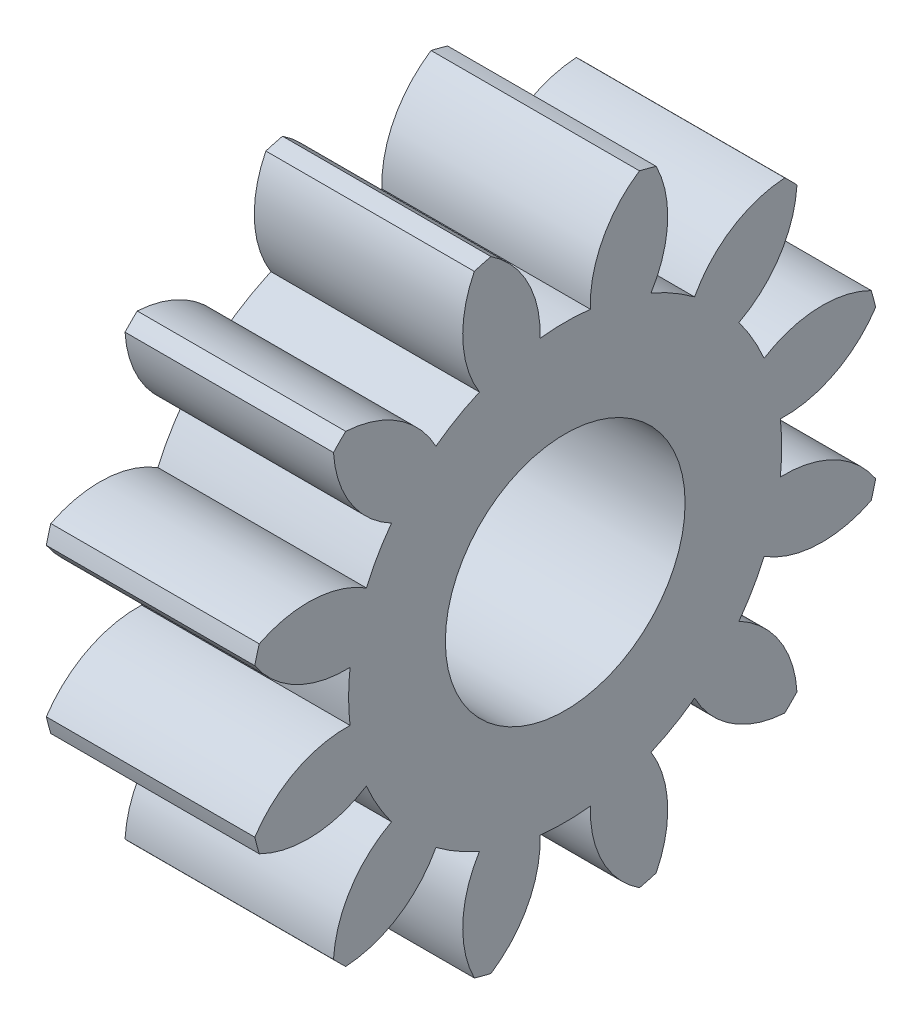
SolidWorks part; units mm, degrees
material "PLA personnalisé"
ref_plane "Plane1" through (0, 0, 0) normal (0, 0, 1) x (1, 0, 0)
ref_plane "Plane2" through (0, 0, 0) normal (0, 1, 0) x (1, 0, 0)
ref_plane "Plane3" through (0, 0, 0) normal (1, 0, 0) x (0, 0, -1)
other "Configuration Table"
sketch "HoldingSke" plane through (0, 0, 0) normal (0, 1, 0) x (1, 0, 0)
  line L0 (0, 0) -> (0.5589, -0.1188)
  line L1 (-15, 0) -> (100, 0) construction
  line L2 (0, 0) -> (-2.1039, 2.3779)
  line L3 (0, 0) -> (-11.863, 4.5341)
  line L4 (0, 0) -> (8.4473, 1.7955)
  line L5 (0, 0) -> (-14.9912, -5.5913)
  line L6 (0, 0) -> (-6.6317, -4.4744)
  line L7 (-2.1039, 2.3779) -> (1.3401, 18.0029)
  line L8 (-76.2, 54.61) -> (-74.8, 54.61)
  line L9 (-71.009, 38.7566) -> (-53.1078, 45.2721)
  line L10 (-76.2, 71.12) -> (104.1128, 71.12)
  line L11 (0, 0) -> (-8, 0)
  line L12 (-76.2, 101.6) -> (-76.147, 101.6)
  line L13 (24.9733, 27.94) -> (52.9518, 28.4284)
  line L14 (24.9733, 27.94) -> (24.9743, 27.94)
  line L15 (24.9733, 27.94) -> (100.4006, 29.5858)
  line L16 (-63.627, -1.75) -> (-12.827, -1.75)
  circle A0 centre (0, 0) radius 4.5
  circle A1 centre (0, 0) radius 8.3115
  circle A2 centre (0, 0) radius 37.5
  circle A3 centre (0, 0) radius 4.5
  dimension "MHD" = 16.623
  dimension "Hub_dia" = 75
  dimension "Bore" = 9
  dimension "MBD" = 9
  dimension "Num_teeth" = 12
  dimension "Pitch" = 0.5714
  dimension "Overall_len" = 16
  dimension "Show_teeth" = 12
  dimension "Thickness" = 8
  dimension "OAL" = 16.0001
  dimension "T_dim" = 1.4
  dimension "Ap" = 20
  dimension "H" = 19.05
  dimension "Pitch_radius" = 180.3128
  dimension "Width" = 8
  dimension "Backlash" = 0.053
  dimension "Addendum_fac" = 1
  dimension "Dedendum_fac" = 1.25
  dimension "Clearance_fac" = 0.25
  dimension "Dedendum_add" = 0.001
  dimension "Module" = 1.75
sketch "BasProSke" plane through (0, 0, 0) normal (0, 1, 0) x (1, 0, 0)
  line L0 (-10, 0) -> (60, 0) construction
  line L1 (0, 0) -> (0, 12.25)
  line L2 (0, 0) -> (8, 0)
  line L3 (8, 0) -> (8, 12.25)
  line L4 (8, 12.25) -> (0, 12.25)
  dimension "Thickness" = 8
  dimension "Diameter" = 24.5
revolve "Base-Revolve" add sketch "BasProSke" angle 360 about L0
sketch "TooCutSke" plane through (0, 0, 0) normal (1, 0, 0) x (0, 0, -1)
  line L1 (0, 0) -> (0, 107) construction
  line L2 (0, 0) -> (-1.4632, 10.3976) construction
  line L3 (0, 0) -> (-5.3948, 20.1337) construction
  line L4 (-1.4632, 10.3976) -> (-2.6974, 10.0668) construction
  arc A0 (0.9651, 8.2553) -> (-0.9651, 8.2553) centre (0, 0) ccw
  arc A1 (2.8783, 11.9332) -> (-2.8783, 11.9332) centre (0, 0) ccw
  circle A2 centre (0, 0) radius 10.5 construction
  circle A3 centre (0, 0) radius 9.8668 construction
  arc A4 (-0.9651, 8.2553) -> (-2.8783, 11.9332) centre (-5.1623, 8.4085) ccw
  arc A5 (2.8783, 11.9332) -> (0.9651, 8.2553) centre (5.1623, 8.4085) ccw
  dimension "Root_dia" = 16.623
  dimension "Overcut_dia" = 24.5508
  dimension "Pitch_dia" = 21
  dimension "Base_dia" = 19.7335
  dimension "Flank_rad" = 4.2
  dimension "Half_ang" = 15
  dimension "Half_CT" = 1.2778
extrude "ToothCut" cut sketch "TooCutSke" along normal through all
fillet "Breaks" [suppressed] radius 0.035
fillet "RootFillets" [suppressed] radius 0.4385
pattern_circular "TeethCuts" count 12 every 30 about axis through (-10, 0, 0) along (1, 0, 0) of "ToothCut", "RootFillets", "Breaks"
sketch "HubNeaOneSke" plane through (0, 0, 0) normal (-1, 0, 0) x (0, 0, 1)
  circle A0 centre (0, 0) radius 8.3115
  dimension "Diameter" = 16.623
extrude "HubNearOne" add sketch "HubNeaOneSke" along normal blind 8.0001
sketch "HubNeaBotSke" plane through (0, 0, 0) normal (-1, 0, 0) x (0, 0, 1)
  circle A0 centre (0, 0) radius 8.3115
  dimension "Diameter" = 16.623
extrude "HubNearBoth" [suppressed] add sketch "HubNeaBotSke" along normal blind 4
ref_plane "FarPln" through (8, 0, 0) normal (1, 0, 0) x (0, 0, -1)
sketch "HubFarSke" plane through (8, 0, 0) normal (1, 0, 0) x (0, 0, -1)
  circle A0 centre (0, 0) radius 8.3115
  dimension "Diameter" = 16.623
extrude "HubFar" [suppressed] add sketch "HubFarSke" along normal blind 4
sketch "BorSke" plane through (0, 0, 0) normal (1, 0, 0) x (0, 0, -1)
  circle A0 centre (0, 0) radius 4.5
  dimension "Diameter" = 9
extrude "Bore" cut sketch "BorSke" along normal mid plane 32.0001
sketch "KeySke" plane through (0, 0, 0) normal (1, 0, 0) x (0, 0, -1)
  line L0 (-1.5, 0) -> (-1.5, 5.9)
  line L1 (-1.5, 5.9) -> (1.5, 5.9)
  line L2 (1.5, 5.9) -> (1.5, 0)
  line L3 (0, 0) -> (0, 34) construction
  line L4 (-1.5, 0) -> (1.5, 0)
  dimension "Offset" = 5.9
  dimension "Width" = 3
extrude "Keyway" [suppressed] cut sketch "KeySke" along normal mid plane 32.0001
pattern_circular "Keyway2" [suppressed] count 2 every 90 about axis through (-10, 0, 0) along (1, 0, 0)
sketch "Esquisse1" plane through (-8.0001, 0, 0) normal (-1, 0, 0) x (0, 0, 1)
  circle A0 centre (0, 0) radius 8.3115
extrude "Enlèv. mat.-Extru.1" cut sketch "Esquisse1" against normal blind 8
sketch "Esquisse2" plane through (8, 0, 0) normal (1, 0, 0) x (0, 0, -1)
  circle A0 centre (0, 0) radius 4.275
  circle A1 centre (0, 0) radius 4.5
  dimension "D1" = 8.55
extrude "Boss.-Extru.1" add sketch "Esquisse2" against normal blind 8
sketch "Esquisse3" plane through (-0.0001, 0, 0) normal (-1, 0, 0) x (0, 0, 1)
  circle A0 centre (0, 0) radius 4.6
  dimension "D1" = 9.2
extrude "Enlèv. mat.-Extru.2" cut sketch "Esquisse3" against normal blind 10
equation "' \"Module@HoldingSke\" = 6.35"
equation "' \"Num_teeth@HoldingSke\" = 12"
equation "' \"Ap@HoldingSke\" =  20"
equation "' \"Ap@HoldingSke\" = 20"
equation "' \"Width@HoldingSke\" = 0.5 * 25.4"
equation "' \"Hub_dia@HoldingSke\"= 1 * 25.4"
equation "' \"Hub_dia@HoldingSke\" = 1 * 25.4"
equation "' \"Overall_len@HoldingSke\" = 1.0 * 25.4"
equation "' \"Bore@HoldingSke\" = 0.75 * 25.4"
equation "' \"T_dim@HoldingSke\" = 0.1 * 25.4"
equation "' \"Width@KeySke\" = 0.25 * 25.4"
equation "' \"Show_teeth@HoldingSke\" = 13"
equation "' \"Backlash@HoldingSke\" = 0.009 * 25.4"
equation "' \"Addendum_fac@HoldingSke\" = 1.0"
equation "' \"Dedendum_fac@HoldingSke\" = 1.25"
equation "' \"Dedendum_add@HoldingSke\" = 0.00005 * 25.4"
equation "' \"Clearance_fac@HoldingSke\" = 0.25"
equation "\"Pitch@HoldingSke\" = 1 / \"Module@HoldingSke\""
equation "\"Overcut_dia@TooCutSke\" = (\"Num_teeth@HoldingSke\" + 2 * \"Addendum_fac@HoldingSke\") / \"Pitch@HoldingSke\" + 0.002 * 25.4"
equation "\"Pitch_dia@TooCutSke\" = \"Num_teeth@HoldingSke\" / \"Pitch@HoldingSke\""
equation "\"Base_dia@TooCutSke\" = \"Num_teeth@HoldingSke\" / \"Pitch@HoldingSke\" * cos((\"Ap@HoldingSke\"  * 3.14159265 / 180))"
equation "\"Root_dia@TooCutSke\" = (\"Num_teeth@HoldingSke\" + 2) / \"Pitch@HoldingSke\" - 2 * (\"Addendum_fac@HoldingSke\" + \"Dedendum_fac@HoldingSke\") / \"Pitch@HoldingSke\" - \"Dedendum_add@HoldingSke\" * 2"
equation "\"Half_ang@TooCutSke\" = 180 / \"Num_teeth@HoldingSke\""
equation "\"Half_CT@TooCutSke\" = \"Num_teeth@HoldingSke\" / \"Pitch@HoldingSke\" * sin((3.14159265 / 2 / \"Num_teeth@HoldingSke\")) / 2 - 7 * \"Backlash@HoldingSke\" / 4"
equation "\"Flank_rad@TooCutSke\" = \"Num_teeth@HoldingSke\" / \"Pitch@HoldingSke\" / 5"
equation "\"Radius@RootFillets\" = \"Clearance_fac@HoldingSke\" / \"Pitch@HoldingSke\" + \"Dedendum_add@HoldingSke\""
equation "\"Break_rad@Breaks\" = 0.02 / \"Pitch@HoldingSke\""
equation "\"Thickness@HoldingSke\" = \"Width@HoldingSke\""
equation "\"OAL@HoldingSke\" = \"Thickness@HoldingSke\""
equation "\"MHD@HoldingSke\" = (\"Num_teeth@HoldingSke\" + 2) / \"Pitch@HoldingSke\" - 2 * (\"Addendum_fac@HoldingSke\" + \"Dedendum_fac@HoldingSke\")  / \"Pitch@HoldingSke\" - \"Dedendum_add@HoldingSke\" * 2"
equation "\"MBD@HoldingSke\" = (\"Num_teeth@HoldingSke\" + 2) / \"Pitch@HoldingSke\" - 2 * (\"Addendum_fac@HoldingSke\" + \"Dedendum_fac@HoldingSke\")  / \"Pitch@HoldingSke\" - \"Dedendum_add@HoldingSke\" * 2 - 0.002 * 25.4"
equation "\"MHD@HoldingSke\" = ((sgn( \"MHD@HoldingSke\" - \"Hub_dia@HoldingSke\" )-1)*( \"MHD@HoldingSke\" - \"Hub_dia@HoldingSke\" ))/-2+ \"Hub_dia@HoldingSke\""
equation "\"MBD@HoldingSke\" = ((sgn( \"MBD@HoldingSke\" - \"Bore@HoldingSke\" )-1)*( \"MBD@HoldingSke\" - \"Bore@HoldingSke\" ))/-2+ \"Bore@HoldingSke\""
equation "\"OAL@HoldingSke\" = ((sgn( \"OAL@HoldingSke\" - \"Overall_len@HoldingSke\" )+1)*( \"OAL@HoldingSke\" - \"Overall_len@HoldingSke\" ))/2 + \"Overall_len@HoldingSke\" + 0.000002 * 25.4"
equation "\"Num_teeth@TeethCuts\" = int( \"Show_teeth@HoldingSke\" ) + 1"
equation "\"Num_teeth@TeethCuts\" = ((sgn( \"Num_teeth@TeethCuts\" - \"Num_teeth@HoldingSke\" )-1)*( \"Num_teeth@TeethCuts\" - \"Num_teeth@HoldingSke\" ))/-2+ \"Num_teeth@HoldingSke\""
equation "\"Num_teeth@TeethCuts\" = ((sgn( \"Num_teeth@TeethCuts\" - 2.0)+1)*( \"Num_teeth@TeethCuts\" - 2.0))/2 +2.0"
equation "\"Angle@TeethCuts\" = 360.0 / \"Num_teeth@HoldingSke\""
equation "\"Diameter@BasProSke\" = (\"Num_teeth@HoldingSke\" + 2 * \"Addendum_fac@HoldingSke\") / \"Pitch@HoldingSke\""
equation "\"Thickness@BasProSke\"  = \"Thickness@HoldingSke\""
equation "' \"Fillet_rad@BasProSke\" =  \"Thickness@HoldingSke\" * 0.05"
equation "' \"Fillet_rad@BasProSke\" = \"Thickness@HoldingSke\" * 0.05"
equation "\"MHD@HoldingSke\" = ((sgn( \"MHD@HoldingSke\" - \"Root_dia@TooCutSke\" )-1)*( \"MHD@HoldingSke\" - \"Root_dia@TooCutSke\" ))/-2+ \"Root_dia@TooCutSke\""
equation "\"Diameter@HubNeaOneSke\" = \"MHD@HoldingSke\""
equation "\"Length@HubNearOne\" = \"OAL@HoldingSke\" - \"Thickness@BasProSke\""
equation "\"Diameter@HubNeaBotSke\" = \"MHD@HoldingSke\""
equation "\"Length@HubNearBoth\" = ( \"OAL@HoldingSke\" - \"Thickness@BasProSke\" ) / 2.0"
equation "\"Thickness@FarPln\" = \"Thickness@BasProSke\""
equation "\"Diameter@HubFarSke\" = \"MHD@HoldingSke\""
equation "\"Length@HubFar\" = ( \"OAL@HoldingSke\" - \"Thickness@BasProSke\" ) / 2.0"
equation "\"Diameter@BorSke\" = \"MBD@HoldingSke\""
equation "\"D1@Bore\" = \"OAL@HoldingSke\" * 2.0"
equation "\"D1@Keyway\" = \"OAL@HoldingSke\" * 2.0"
equation "\"Offset@KeySke\" = \"T_dim@HoldingSke\" + \"MBD@HoldingSke\" / 2.0"
